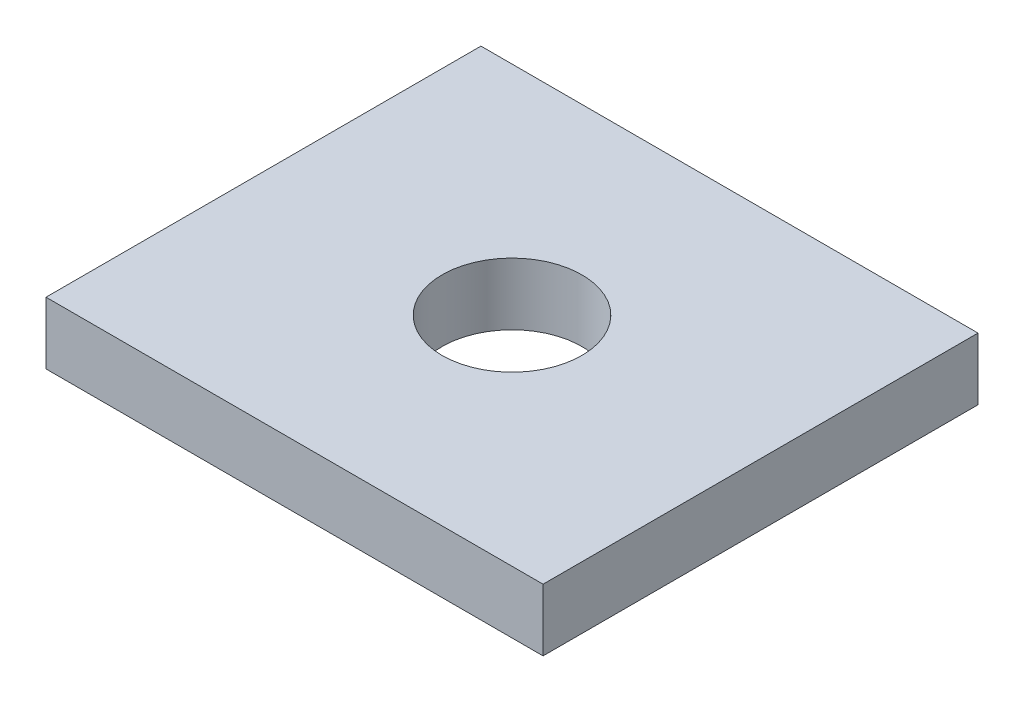
SolidWorks part; units mm, degrees
ref_plane "Front Plane" through (0, 0, 0) normal (0, 0, 1) x (1, 0, 0)
ref_plane "Top Plane" through (0, 0, 0) normal (0, 1, 0) x (1, 0, 0)
ref_plane "Right Plane" through (0, 0, 0) normal (1, 0, 0) x (0, 0, -1)
sketch "Sketch1" plane through (0, 0, 0) normal (0, 1, 0) x (1, 0, 0)
  line L0 (-12.7, 11.1125) -> (12.7, 11.1125)
  line L1 (12.7, 11.1125) -> (12.7, -11.1125)
  line L2 (12.7, -11.1125) -> (-12.7, -11.1125)
  line L3 (-12.7, -11.1125) -> (-12.7, 11.1125)
  line L4 (12.7, 11.1125) -> (-12.7, -11.1125) construction
  point P2 (0, 0)
extrude "Extrude1" add sketch "Sketch1" along normal mid plane 3.175
sketch "Sketch2" plane through (0, 1.5875, 0) normal (0, 1, 0) x (1, 0, 0)
  circle A0 centre (0, 0) radius 3.5719
  dimension "D1" = 7.1437
extrude "Cut-Extrude1" cut sketch "Sketch2" against normal through all
